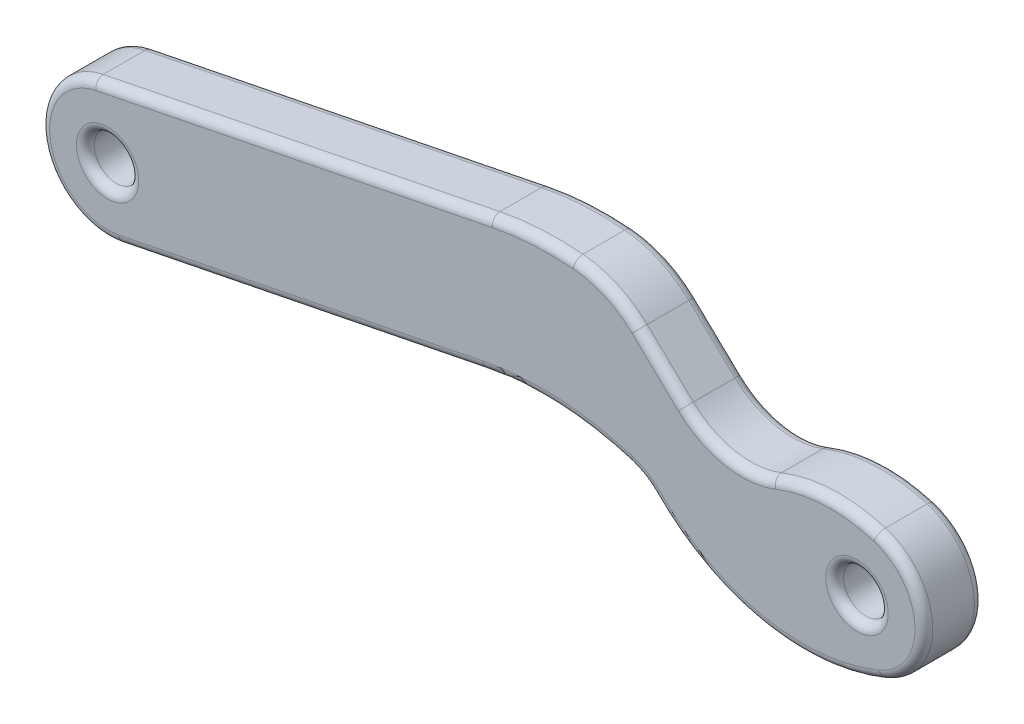
SolidWorks part; units mm, degrees
ref_plane "Front" through (0, 0, 0) normal (0, 0, 1) x (1, 0, 0)
ref_plane "Top" through (0, 0, 0) normal (0, 1, 0) x (1, 0, 0)
ref_plane "Right" through (0, 0, 0) normal (1, 0, 0) x (0, 0, -1)
sketch "Sketch1" plane through (0, 0, 0) normal (0, 0, 1) x (1, 0, 0)
  line L0 (0, 0) -> (25.2125, 0) construction
  line L1 (0, 2.25) -> (25.2125, 2.25)
  line L2 (0, -2.25) -> (25.2125, -2.25)
  circle A0 centre (0, 0) radius 0.75
  arc A1 (0, 2.25) -> (0, -2.25) centre (0, 0) ccw
  arc A2 (25.2125, -2.25) -> (25.2125, 2.25) centre (25.2125, 0) ccw
  circle A3 centre (25.2125, 0) radius 0.75
  point P3 (12.6062, 0)
  dimension "D1" = 1.5
  dimension "D2" = 25.2125
  dimension "D3" = 1.5
extrude "Boss-Extrude1" add sketch "Sketch1" along normal blind 2
sketch "Sketch2" plane through (0, 0, 0) normal (0, 0, 1) x (1, 0, 0)
  line L0 (12.0571, -0.5571) -> (14.4503, 0.4122)
  line L1 (15.3955, 0.2207) -> (16.4724, -0.5571)
  line L2 (16.4724, -0.5571) -> (17.3174, -2.6432)
  line L3 (17.3174, -2.6432) -> (12.0571, -3.2881)
  line L4 (12.0571, -3.2881) -> (12.0571, -0.5571)
  arc A0 (14.4503, 0.4122) -> (15.3955, 0.2207) centre (14.7783, -0.3977) cw
sketch "Sketch3" plane through (0, 0, 0) normal (0, 0, 1) x (1, 0, 0)
  line L0 (0.4422, -2.2061) -> (12.6762, 0.246)
  line L1 (17.5603, 0) -> (24.5509, -2.1505)
  line L2 (-0.4422, 2.2061) -> (12.8988, 4.8801)
  line L3 (17.8044, 4.633) -> (25.874, 2.1505)
  circle A0 centre (0, 0) radius 2.25 construction
  arc A1 (12.6762, 0.246) -> (17.5603, 0) centre (14.6328, -9.5162) cw
  arc A2 (24.5509, -2.1505) -> (25.874, 2.1505) centre (25.2125, 0) ccw
  arc A3 (25.2125, -2.25) -> (25.2125, 2.25) centre (25.2125, 0) ccw construction
  circle A4 centre (25.2125, 0) radius 0.75 construction
  arc A5 (0.4422, -2.2061) -> (-0.4422, 2.2061) centre (0, 0) cw
  arc A6 (0, 2.25) -> (0, -2.25) centre (0, 0) ccw construction
  arc A7 (12.8988, 4.8801) -> (17.8044, 4.633) centre (14.864, -4.9249) cw
  point P17 (0, 0)
  point P24 (17.5603, 0)
  dimension "D1" = 10
extrude "Cut-Extrude4" cut sketch "Sketch3" along normal through all flip side to cut
sketch "Sketch4" plane through (0, 0, 2) normal (0, 0, 1) x (1, 0, 0)
  line L4 (12.8988, 4.8801) -> (-0.4422, 2.2061)
  line L5 (25.874, 2.1505) -> (17.8044, 4.633)
  line L6 (17.5603, 0) -> (24.5509, -2.1505)
  line L7 (0.4422, -2.2061) -> (12.6762, 0.246)
  line L8 (12.8988, 4.8801) -> (-0.4422, 2.2061)
  line L9 (25.874, 2.1505) -> (17.8044, 4.633)
  line L10 (17.5603, 0) -> (24.5509, -2.1505)
  line L11 (0.4422, -2.2061) -> (12.6762, 0.246)
  circle A0 centre (25.2125, 0) radius 0.75 construction
  circle A1 centre (0, 0) radius 0.75 construction
  circle A2 centre (25.2125, 0) radius 0.75
  circle A3 centre (0, 0) radius 0.75
  arc A4 (17.8044, 4.633) -> (12.8988, 4.8801) centre (14.864, -4.9249) ccw
  arc A5 (24.5509, -2.1505) -> (25.874, 2.1505) centre (25.2125, 0) ccw
  arc A6 (17.5603, 0) -> (12.6762, 0.246) centre (14.6328, -9.5162) ccw
  arc A7 (-0.4422, 2.2061) -> (0.4422, -2.2061) centre (0, 0) ccw
  arc A8 (17.8044, 4.633) -> (12.8988, 4.8801) centre (14.864, -4.9249) ccw
  arc A9 (24.5509, -2.1505) -> (25.874, 2.1505) centre (25.2125, 0) ccw
  arc A10 (17.5603, 0) -> (12.6762, 0.246) centre (14.6328, -9.5162) ccw
  arc A11 (-0.4422, 2.2061) -> (0.4422, -2.2061) centre (0, 0) ccw
  dimension "D1" = 0
extrude "Boss-Extrude2" add sketch "Sketch4" against normal up to vertex
sketch3d "3DSketch2"
  line L8 (28.5539, 2.4862, 2) -> (20.7366, 4.2679, 2)
  line L9 (30.5553, 5.4776, 2) -> (31.9718, 1.7671, 2)
  line L10 (18.1052, 9.4862, 2) -> (17.7608, 10.5197, 2)
  line L11 (20.8202, 8.9829, 2) -> (18.1052, 9.4862, 2)
  arc A18 (30.4787, 0.5435, 2) -> (28.5539, 2.4862, 2) centre (27.9872, 0, 2) ccw
  arc A19 (29.7103, 7.668, 2) -> (30.5553, 5.4776, 2) centre (-281.7577, -113.7456, 2) ccw
  arc A20 (25.106, 12.1538, 2) -> (29.7103, 7.668, 2) centre (22.4753, 4.8477, 2) ccw
  arc A21 (21.1241, 8.8735, 2) -> (20.8202, 8.9829, 2) centre (20.6379, 7.9997, 2) ccw
  arc A22 (26.5449, 8.4396, 2) -> (21.1241, 8.8735, 2) centre (23.5636, 5.2719, 2) ccw
  arc A23 (25.3798, 7.2017, 2) -> (26.5449, 8.4396, 2) centre (25.9623, 7.8207, 2) ccw
  arc A24 (21.6394, 7.094, 2) -> (25.3798, 7.2017, 2) centre (23.5636, 5.2719, 2) ccw
  arc A25 (20.9991, 6.8287, 2) -> (21.6394, 7.094, 2) centre (21.0222, 7.6784, 2) ccw
  arc A26 (20.7366, 4.2679, 2) -> (20.9991, 6.8287, 2) centre (23.5636, 5.2719, 2) ccw
  spline S12 degree 3 poles (31.0836, 0.7536, 2) (30.8819, 0.6835, 2) (30.6803, 0.6135, 2) (30.4787, 0.5435, 2) knots 0 0 0 0 1 1 1 1
  spline S13 degree 3 poles (31.9718, 1.7671, 2) (31.9394, 1.656, 2) (31.8982, 1.5432, 2) (31.793, 1.3329, 2) (31.7287, 1.2339, 2) (31.5778, 1.0565, 2) (31.4894, 0.9764, 2) (31.2983, 0.8449, 2) (31.195, 0.7923, 2) (31.0836, 0.7536, 2) knots 0 0 0 0 0.25 0.25 0.5 0.5 0.75 0.75 1 1 1 1
  spline S14 degree 3 poles (21.9785, 12.5206, 2) (22.5054, 12.5209, 2) (23.0298, 12.4877, 2) (24.0747, 12.3695, 2) (24.5956, 12.2784, 2) (25.106, 12.1538, 2) knots 0 0 0 0 0.5 0.5 1 1 1 1
  spline S15 degree 3 poles (21.2302, 12.2749, 2) (21.4793, 12.3579, 2) (21.7264, 12.4476, 2) (21.9785, 12.5206, 2) knots 0 0 0 0 1 1 1 1
  spline S16 degree 3 poles (19.5527, 11.5132, 2) (19.7933, 11.7049, 2) (20.0675, 11.854, 2) (20.6399, 12.0887, 2) (20.9367, 12.1771, 2) (21.2302, 12.2749, 2) knots 0 0 0 0 0.5 0.5 1 1 1 1
  spline S17 degree 3 poles (17.7608, 10.5197, 2) (18.4099, 10.7525, 2) (19.009, 11.0801, 2) (19.5527, 11.5132, 2) knots 0 0 0 0 1 1 1 1
  point P53 (27.9872, 0, 4.55)
  point P54 (-281.7577, -113.7456, -332.2957)
  point P55 (22.4753, 4.8477, -5.7653)
  point P56 (20.6379, 7.9997, 3)
  point P57 (23.5636, 5.2719, 6.35)
  point P58 (25.9623, 7.8207, 2.85)
  point P59 (23.5636, 5.2719, -0.65)
  point P60 (21.0222, 7.6784, 2.85)
  point P61 (23.5636, 5.2719, -1)
sketch3d "3DSketch4"
  line L10 (25.9622, 2.4373, -2.25) -> (24.0428, 3.0278, -2.25)
  line L11 (24.9152, -6.1786, -2.25) -> (27.4825, -1.1616, -2.25)
  line L12 (15.6641, -5.7047, -2.25) -> (24.9152, -6.1786, -2.25)
  line L13 (15.6125, 5.6212, -2.25) -> (15.6641, -5.7047, -2.25)
  line L14 (18.2168, 4.82, -2.25) -> (15.6125, 5.6212, -2.25)
  arc A8 (27.4825, -1.1616, -2.25) -> (25.9622, 2.4373, -2.25) centre (25.2125, 0, -2.25) ccw
  arc A9 (18.8996, 4.0782, -2.25) -> (18.2168, 4.82, -2.25) centre (17.9228, 3.8643, -2.25) ccw
  arc A10 (23.061, 2.798, -2.25) -> (18.8996, 4.0782, -2.25) centre (21.3418, 4.6129, -2.25) ccw
  arc A11 (24.0428, 3.0278, -2.25) -> (23.061, 2.798, -2.25) centre (23.7487, 2.072, -2.25) ccw
  point P25 (25.2125, 0, 0.3)
  point P26 (17.9228, 3.8643, -1.25)
  point P27 (21.3418, 4.6129, -4.75)
  point P28 (23.7487, 2.072, -1.25)
sketch "Sketch6" plane through (0, 0, 0) normal (0, 0, 1) x (1, 0, 0)
  line L6 (15.6981, 5.0403) -> (20.7359, 8.302)
  line L7 (20.7359, 8.302) -> (25.874, 2.1505)
  line L8 (17.8547, 4.0701) -> (19.4088, 2.5872)
  arc A5 (19.4088, 2.5872) -> (22.3758, 2.0109) centre (21.3418, 4.6129) ccw
  arc A6 (18.8996, 4.0782) -> (23.061, 2.798) centre (21.3418, 4.6129) ccw construction
  arc A7 (17.8547, 4.0701) -> (15.6981, 5.0403) centre (15.4018, 1.4995) ccw
  arc A8 (17.8044, 4.633) -> (12.8988, 4.8801) centre (14.864, -4.9249) ccw construction
  arc A9 (22.3758, 2.0109) -> (25.874, 2.1505) centre (24.3234, -2.89) cw
  arc A10 (24.5509, -2.1505) -> (25.874, 2.1505) centre (25.2125, 0) ccw construction
  arc A11 (26.0683, -2.0809) -> (18.3674, -0.4923) centre (23.3949, 4.4193) cw construction
  arc A12 (17.5603, 0) -> (18.3674, -0.4923) centre (16.997, -1.8312) cw construction
  arc A13 (17.5603, 0) -> (12.6762, 0.246) centre (14.6328, -9.5162) ccw construction
  point P20 (17.8547, 4.0701)
  dimension "D1" = 0.3
extrude "Cut-Extrude6" cut sketch "Sketch6" along normal through all and the other way through all
sketch "Sketch7" plane through (0, 0, 2) normal (0, 0, 1) x (1, 0, 0)
  line L0 (17.5603, 0) -> (19.4665, 0.5655)
  line L1 (19.4665, 0.5655) -> (26.0683, -2.0809)
  arc A0 (18.3674, -0.4923) -> (17.5603, 0) centre (16.997, -1.8312) ccw construction
  arc A1 (18.3674, -0.4923) -> (26.0683, -2.0809) centre (23.3949, 4.4193) ccw construction
  arc A2 (18.3674, -0.4923) -> (17.5603, 0) centre (16.997, -1.8312) ccw
  arc A3 (18.3674, -0.4923) -> (26.0683, -2.0809) centre (23.3949, 4.4193) ccw
extrude "Boss-Extrude3" add sketch "Sketch7" against normal up to vertex (2 mm away) up to point (17.5603, 0, 0)
fillet "Fillet1" radius 0.3 28 edges at (25.9625, 0, 0) (0.75, 0, 0) (6.5592, -0.9801, 0) (15.1336, 0.4275, 0) (14.2928, 5.0588, 2) (14.2928, 5.0588, 0) (6.2283, 3.5431, 2) (6.2283, 3.5431, 0) (-2.2061, -0.4422, 0) (25.9625, 0, 2) (0.75, 0, 2) (27.4601, 0.1032, 2) (15.1336, 0.4275, 2) (6.5592, -0.9801, 2) (-2.2061, -0.4422, 2) (20.8079, 1.8643, 0) (16.8595, 4.7398, 0) (24.113, 2.3795, 2) (16.8595, 4.7398, 2) (20.8079, 1.8643, 2) (21.9749, -2.4642, 2) (21.9749, -2.4642, 0) (17.9947, -0.1956, 2) (17.9947, -0.1956, 0) (18.6317, 3.3287, 0) (18.6317, 3.3287, 2)
